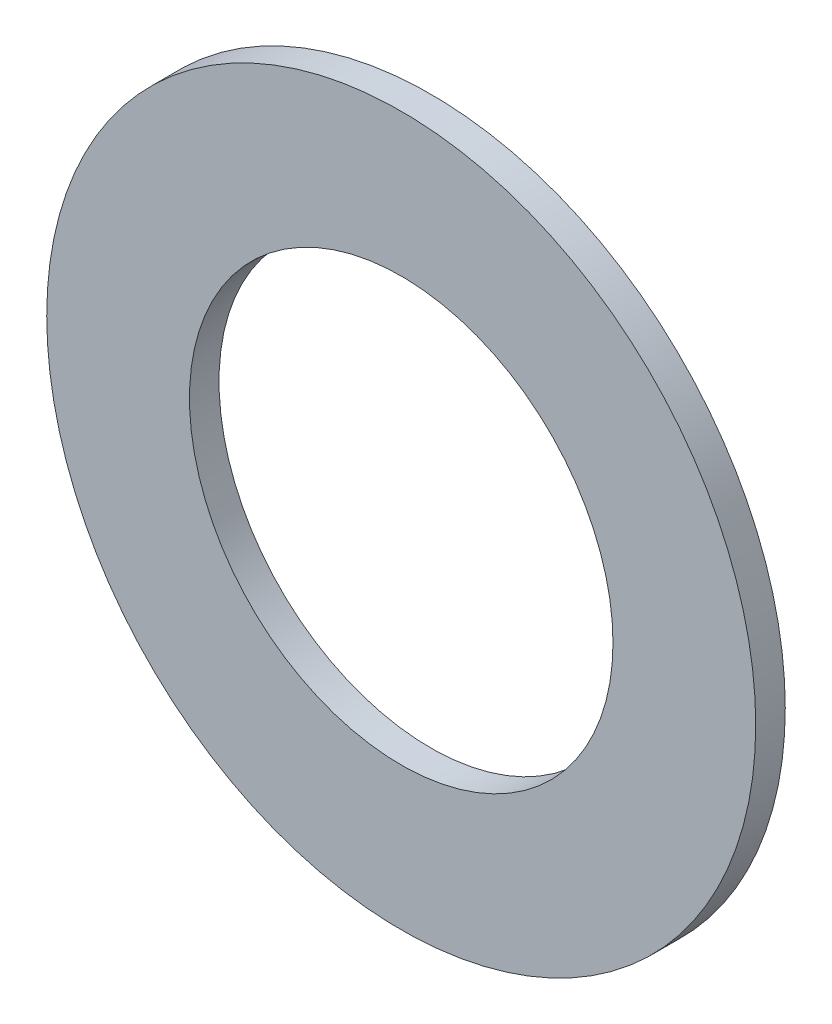
SolidWorks part; units mm, degrees
ref_plane "Front Plane" through (0, 0, 0) normal (0, 0, 1) x (1, 0, 0)
ref_plane "Top Plane" through (0, 0, 0) normal (0, 1, 0) x (1, 0, 0)
ref_plane "Right Plane" through (0, 0, 0) normal (1, 0, 0) x (0, 0, -1)
sketch "Sketch1" plane through (0, 0, 0) normal (0, 0, 1) x (1, 0, 0)
  circle A0 centre (0, 0) radius 19.05
  circle A1 centre (0, 0) radius 11.3792
  dimension "D1" = 38.1
  dimension "ID" = 22.7584
extrude "Extrude1" add sketch "Sketch1" along normal mid plane 1.5875
sketch "Sketch2" plane through (0, 0, 0) normal (1, 0, 0) x (0, 0, -1)
  line L0 (-0.7937, -11.3792) -> (0.7937, -11.3792) construction
  line L3 (0.7937, 11.3792) -> (-0.7937, 11.3792) construction
  line L5 (-0.7937, -11.3792) -> (0.7937, -11.3792)
  line L6 (0.7937, 11.3792) -> (-0.7937, 11.3792)
sketch "Sketch4" plane through (0, 0, 0.7937) normal (0, 0, 1) x (1, 0, 0)
  line L0 (0, 0) -> (-8.0463, 8.0463)
  line L1 (0, -1.7463) -> (0, 1.7463) construction
  circle A0 centre (0, 0) radius 11.3792 construction
  dimension "D1" = 45
